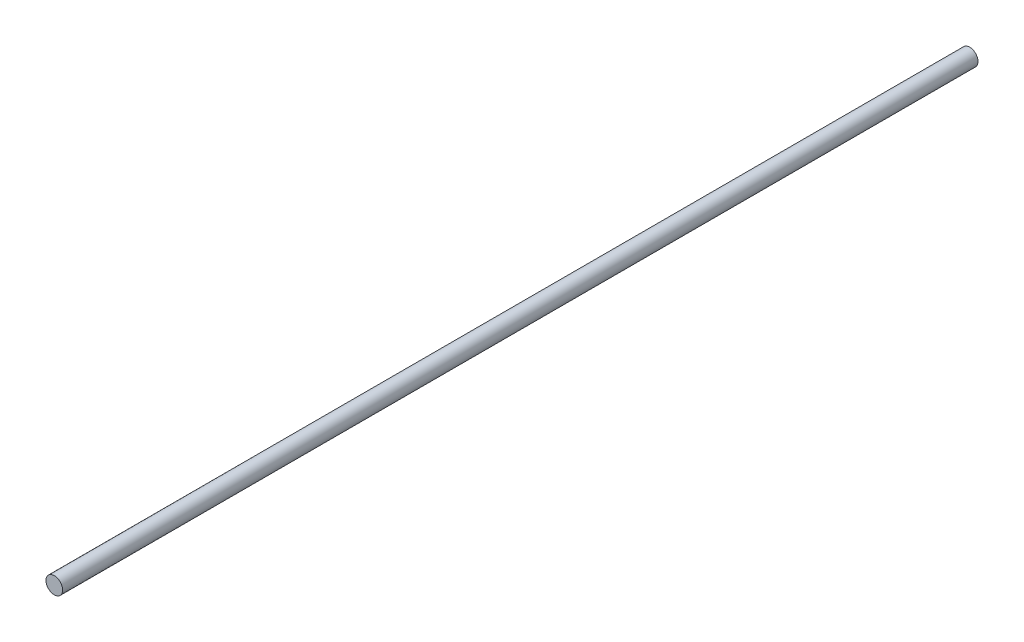
SolidWorks part; units mm, degrees
ref_plane "Plan de face" through (0, 0, 0) normal (0, 0, 1) x (1, 0, 0)
ref_plane "Plan de dessus" through (0, 0, 0) normal (0, 1, 0) x (1, 0, 0)
ref_plane "Plan de droite" through (0, 0, 0) normal (1, 0, 0) x (0, 0, -1)
sketch "Esquisse1" plane through (0, 0, 0) normal (0, 0, 1) x (1, 0, 0)
  circle A0 centre (0, 0) radius 4
  dimension "D1" = 8
extrude "Boss.-Extru.1" add sketch "Esquisse1" along normal blind 440
